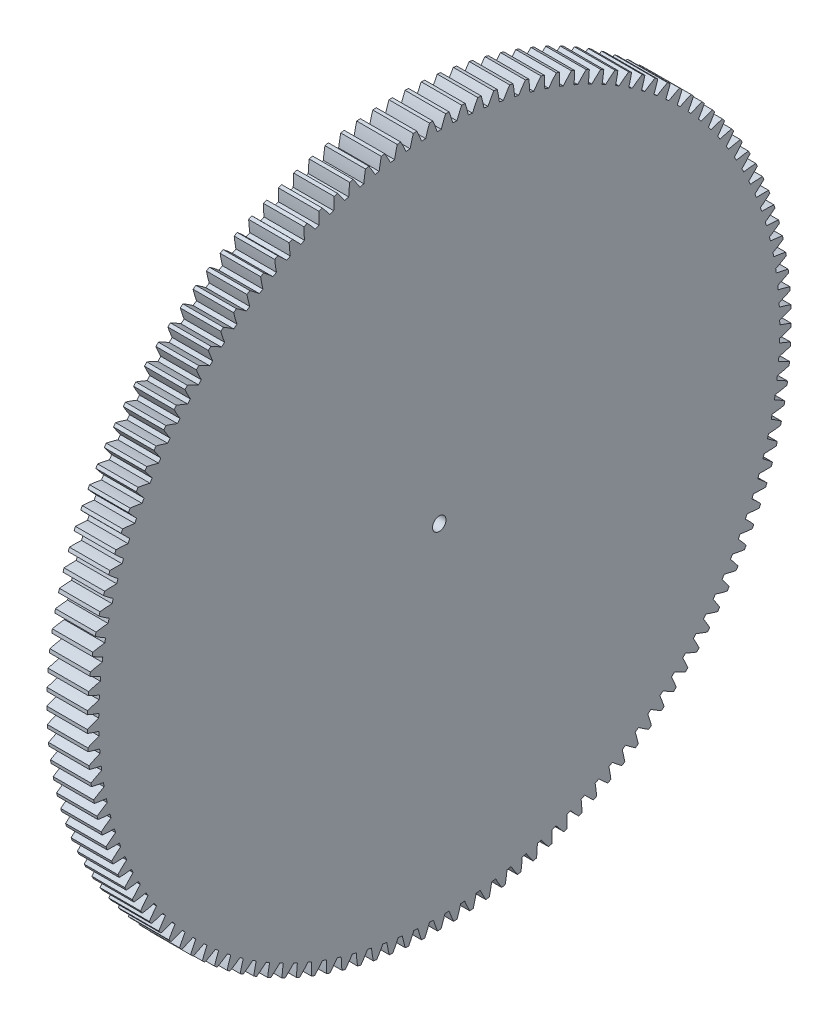
SolidWorks part; units mm, degrees
ref_plane "Plane1" through (0, 0, 0) normal (0, 0, 1) x (1, 0, 0)
ref_plane "Plane2" through (0, 0, 0) normal (0, 1, 0) x (1, 0, 0)
ref_plane "Plane3" through (0, 0, 0) normal (1, 0, 0) x (0, 0, -1)
sketch "HoldingSke" plane through (0, 0, 0) normal (0, 1, 0) x (1, 0, 0)
  line L0 (0, 0) -> (-0.4876, -0.4547)
  line L1 (-15, 0) -> (100, 0) construction
  line L2 (0, 0) -> (-2.1039, 2.3779)
  line L3 (0, 0) -> (-11.863, 4.5341)
  line L4 (0, 0) -> (-6.316, 5.8897)
  line L5 (0, 0) -> (-46.8476, -17.4728)
  line L6 (0, 0) -> (-9.9476, -6.7116)
  line L7 (-2.1039, 2.3779) -> (8.6586, 51.2059)
  line L8 (-76.2, 54.61) -> (-75.5, 54.61)
  line L9 (-71.009, 38.7566) -> (-53.1078, 45.2721)
  line L10 (-76.2, 71.12) -> (104.1128, 71.12)
  line L11 (0, 0) -> (-12, 0)
  line L12 (-76.2, 101.6) -> (-76.147, 101.6)
  line L13 (24.9733, 27.94) -> (52.9518, 28.4284)
  line L14 (24.9733, 27.94) -> (24.9743, 27.94)
  line L15 (24.9733, 27.94) -> (100.4006, 29.5858)
  line L16 (-63.627, -1.5) -> (-12.827, -1.5)
  circle A0 centre (0, 0) radius 2
  circle A1 centre (0, 0) radius 37.5
  circle A2 centre (0, 0) radius 37.5
  circle A3 centre (0, 0) radius 2
  dimension "MHD" = 75
  dimension "Hub_dia" = 75
  dimension "Bore" = 4
  dimension "MBD" = 4
  dimension "Num_teeth" = 137
  dimension "Pitch" = 0.6667
  dimension "Overall_len" = 50
  dimension "Show_teeth" = 137
  dimension "Thickness" = 12
  dimension "OAL" = 50.0001
  dimension "T_dim" = 0.7
  dimension "Ap" = 20
  dimension "H" = 19.05
  dimension "Pitch_radius" = 180.3128
  dimension "Width" = 12
  dimension "Backlash" = 0.053
  dimension "Addendum_fac" = 1
  dimension "Dedendum_fac" = 1.25
  dimension "Clearance_fac" = 0.25
  dimension "Dedendum_add" = 0.001
  dimension "Module" = 1.5
sketch "BasProSke" plane through (0, 0, 0) normal (0, 1, 0) x (1, 0, 0)
  line L0 (-10, 0) -> (60, 0) construction
  line L1 (0, 0) -> (0, 104.25)
  line L2 (0, 0) -> (12, 0)
  line L3 (12, 0) -> (12, 104.25)
  line L4 (12, 104.25) -> (0, 104.25)
  dimension "Thickness" = 12
  dimension "Diameter" = 208.5
revolve "Base-Revolve" add sketch "BasProSke" angle 360 about L0
sketch "TooCutSke" plane through (0, 0, 0) normal (1, 0, 0) x (0, 0, -1)
  line L1 (0, 0) -> (0, 107) construction
  line L2 (0, 0) -> (-1.2708, 102.7421) construction
  line L3 (0, 0) -> (-4.7117, 205.4345) construction
  line L4 (-1.2708, 102.7421) -> (-2.3559, 102.7173) construction
  arc A0 (0.6056, 100.8722) -> (-0.6056, 100.8722) centre (0, 0) ccw
  arc A1 (1.8867, 104.2583) -> (-1.8867, 104.2583) centre (0, 0) ccw
  circle A2 centre (0, 0) radius 102.75 construction
  circle A3 centre (0, 0) radius 96.5534 construction
  arc A4 (-0.6056, 100.8722) -> (-1.8867, 104.2583) centre (-39.6499, 88.0366) ccw
  arc A5 (1.8867, 104.2583) -> (0.6056, 100.8722) centre (39.6499, 88.0366) ccw
  dimension "Root_dia" = 201.748
  dimension "Overcut_dia" = 208.5508
  dimension "Pitch_dia" = 205.5
  dimension "Base_dia" = 193.1068
  dimension "Flank_rad" = 41.1
  dimension "Half_ang" = 1.314
  dimension "Half_CT" = 1.0853
extrude "ToothCut" cut sketch "TooCutSke" along normal through all
fillet "Breaks" [suppressed] radius 0.03
fillet "RootFillets" [suppressed] radius 0.376
pattern_circular "TeethCuts" count 137 every 2.628 about axis through (-10, 0, 0) along (1, 0, 0) of "ToothCut", "RootFillets", "Breaks"
sketch "HubNeaOneSke" plane through (0, 0, 0) normal (-1, 0, 0) x (0, 0, 1)
  circle A0 centre (0, 0) radius 37.5
  dimension "Diameter" = 75
extrude "HubNearOne" [suppressed] add sketch "HubNeaOneSke" along normal blind 38.0001
sketch "HubNeaBotSke" plane through (0, 0, 0) normal (-1, 0, 0) x (0, 0, 1)
  circle A0 centre (0, 0) radius 37.5
  dimension "Diameter" = 75
extrude "HubNearBoth" [suppressed] add sketch "HubNeaBotSke" along normal blind 19
ref_plane "FarPln" through (12, 0, 0) normal (1, 0, 0) x (0, 0, -1)
sketch "HubFarSke" plane through (12, 0, 0) normal (1, 0, 0) x (0, 0, -1)
  circle A0 centre (0, 0) radius 37.5
  dimension "Diameter" = 75
extrude "HubFar" [suppressed] add sketch "HubFarSke" along normal blind 19
sketch "BorSke" plane through (0, 0, 0) normal (1, 0, 0) x (0, 0, -1)
  circle A0 centre (0, 0) radius 2
  dimension "Diameter" = 4
extrude "Bore" cut sketch "BorSke" along normal mid plane 100.0001
sketch "KeySke" plane through (0, 0, 0) normal (1, 0, 0) x (0, 0, -1)
  line L0 (-0.8, 0) -> (-0.8, 2.7)
  line L1 (-0.8, 2.7) -> (0.8, 2.7)
  line L2 (0.8, 2.7) -> (0.8, 0)
  line L3 (0, 0) -> (0, 34) construction
  line L4 (-0.8, 0) -> (0.8, 0)
  dimension "Offset" = 2.7
  dimension "Width" = 1.6
extrude "Keyway" [suppressed] cut sketch "KeySke" along normal mid plane 100.0001
pattern_circular "Keyway2" [suppressed] count 2 every 90 about axis through (-10, 0, 0) along (1, 0, 0)
equation "' \"Module@HoldingSke\" = 6.35"
equation "' \"Num_teeth@HoldingSke\" = 12"
equation "' \"Ap@HoldingSke\" =  20"
equation "' \"Ap@HoldingSke\" = 20"
equation "' \"Width@HoldingSke\" = 0.5 * 25.4"
equation "' \"Hub_dia@HoldingSke\"= 1 * 25.4"
equation "' \"Hub_dia@HoldingSke\" = 1 * 25.4"
equation "' \"Overall_len@HoldingSke\" = 1.0 * 25.4"
equation "' \"Bore@HoldingSke\" = 0.75 * 25.4"
equation "' \"T_dim@HoldingSke\" = 0.1 * 25.4"
equation "' \"Width@KeySke\" = 0.25 * 25.4"
equation "' \"Show_teeth@HoldingSke\" = 13"
equation "' \"Backlash@HoldingSke\" = 0.009 * 25.4"
equation "' \"Addendum_fac@HoldingSke\" = 1.0"
equation "' \"Dedendum_fac@HoldingSke\" = 1.25"
equation "' \"Dedendum_add@HoldingSke\" = 0.00005 * 25.4"
equation "' \"Clearance_fac@HoldingSke\" = 0.25"
equation "\"Pitch@HoldingSke\" = 1 / \"Module@HoldingSke\""
equation "\"Overcut_dia@TooCutSke\" = (\"Num_teeth@HoldingSke\" + 2 * \"Addendum_fac@HoldingSke\") / \"Pitch@HoldingSke\" + 0.002 * 25.4"
equation "\"Pitch_dia@TooCutSke\" = \"Num_teeth@HoldingSke\" / \"Pitch@HoldingSke\""
equation "\"Base_dia@TooCutSke\" = \"Num_teeth@HoldingSke\" / \"Pitch@HoldingSke\" * cos((\"Ap@HoldingSke\"  * 3.14159265 / 180))"
equation "\"Root_dia@TooCutSke\" = (\"Num_teeth@HoldingSke\" + 2) / \"Pitch@HoldingSke\" - 2 * (\"Addendum_fac@HoldingSke\" + \"Dedendum_fac@HoldingSke\") / \"Pitch@HoldingSke\" - \"Dedendum_add@HoldingSke\" * 2"
equation "\"Half_ang@TooCutSke\" = 180 / \"Num_teeth@HoldingSke\""
equation "\"Half_CT@TooCutSke\" = \"Num_teeth@HoldingSke\" / \"Pitch@HoldingSke\" * sin((3.14159265 / 2 / \"Num_teeth@HoldingSke\")) / 2 - 7 * \"Backlash@HoldingSke\" / 4"
equation "\"Flank_rad@TooCutSke\" = \"Num_teeth@HoldingSke\" / \"Pitch@HoldingSke\" / 5"
equation "\"Radius@RootFillets\" = \"Clearance_fac@HoldingSke\" / \"Pitch@HoldingSke\" + \"Dedendum_add@HoldingSke\""
equation "\"Break_rad@Breaks\" = 0.02 / \"Pitch@HoldingSke\""
equation "\"Thickness@HoldingSke\" = \"Width@HoldingSke\""
equation "\"OAL@HoldingSke\" = \"Thickness@HoldingSke\""
equation "\"MHD@HoldingSke\" = (\"Num_teeth@HoldingSke\" + 2) / \"Pitch@HoldingSke\" - 2 * (\"Addendum_fac@HoldingSke\" + \"Dedendum_fac@HoldingSke\")  / \"Pitch@HoldingSke\" - \"Dedendum_add@HoldingSke\" * 2"
equation "\"MBD@HoldingSke\" = (\"Num_teeth@HoldingSke\" + 2) / \"Pitch@HoldingSke\" - 2 * (\"Addendum_fac@HoldingSke\" + \"Dedendum_fac@HoldingSke\")  / \"Pitch@HoldingSke\" - \"Dedendum_add@HoldingSke\" * 2 - 0.002 * 25.4"
equation "\"MHD@HoldingSke\" = ((sgn( \"MHD@HoldingSke\" - \"Hub_dia@HoldingSke\" )-1)*( \"MHD@HoldingSke\" - \"Hub_dia@HoldingSke\" ))/-2+ \"Hub_dia@HoldingSke\""
equation "\"MBD@HoldingSke\" = ((sgn( \"MBD@HoldingSke\" - \"Bore@HoldingSke\" )-1)*( \"MBD@HoldingSke\" - \"Bore@HoldingSke\" ))/-2+ \"Bore@HoldingSke\""
equation "\"OAL@HoldingSke\" = ((sgn( \"OAL@HoldingSke\" - \"Overall_len@HoldingSke\" )+1)*( \"OAL@HoldingSke\" - \"Overall_len@HoldingSke\" ))/2 + \"Overall_len@HoldingSke\" + 0.000002 * 25.4"
equation "\"Num_teeth@TeethCuts\" = int( \"Show_teeth@HoldingSke\" ) + 1"
equation "\"Num_teeth@TeethCuts\" = ((sgn( \"Num_teeth@TeethCuts\" - \"Num_teeth@HoldingSke\" )-1)*( \"Num_teeth@TeethCuts\" - \"Num_teeth@HoldingSke\" ))/-2+ \"Num_teeth@HoldingSke\""
equation "\"Num_teeth@TeethCuts\" = ((sgn( \"Num_teeth@TeethCuts\" - 2.0)+1)*( \"Num_teeth@TeethCuts\" - 2.0))/2 +2.0"
equation "\"Angle@TeethCuts\" = 360.0 / \"Num_teeth@HoldingSke\""
equation "\"Diameter@BasProSke\" = (\"Num_teeth@HoldingSke\" + 2 * \"Addendum_fac@HoldingSke\") / \"Pitch@HoldingSke\""
equation "\"Thickness@BasProSke\"  = \"Thickness@HoldingSke\""
equation "' \"Fillet_rad@BasProSke\" =  \"Thickness@HoldingSke\" * 0.05"
equation "' \"Fillet_rad@BasProSke\" = \"Thickness@HoldingSke\" * 0.05"
equation "\"MHD@HoldingSke\" = ((sgn( \"MHD@HoldingSke\" - \"Root_dia@TooCutSke\" )-1)*( \"MHD@HoldingSke\" - \"Root_dia@TooCutSke\" ))/-2+ \"Root_dia@TooCutSke\""
equation "\"Diameter@HubNeaOneSke\" = \"MHD@HoldingSke\""
equation "\"Length@HubNearOne\" = \"OAL@HoldingSke\" - \"Thickness@BasProSke\""
equation "\"Diameter@HubNeaBotSke\" = \"MHD@HoldingSke\""
equation "\"Length@HubNearBoth\" = ( \"OAL@HoldingSke\" - \"Thickness@BasProSke\" ) / 2.0"
equation "\"Thickness@FarPln\" = \"Thickness@BasProSke\""
equation "\"Diameter@HubFarSke\" = \"MHD@HoldingSke\""
equation "\"Length@HubFar\" = ( \"OAL@HoldingSke\" - \"Thickness@BasProSke\" ) / 2.0"
equation "\"Diameter@BorSke\" = \"MBD@HoldingSke\""
equation "\"D1@Bore\" = \"OAL@HoldingSke\" * 2.0"
equation "\"D1@Keyway\" = \"OAL@HoldingSke\" * 2.0"
equation "\"Offset@KeySke\" = \"T_dim@HoldingSke\" + \"MBD@HoldingSke\" / 2.0"
